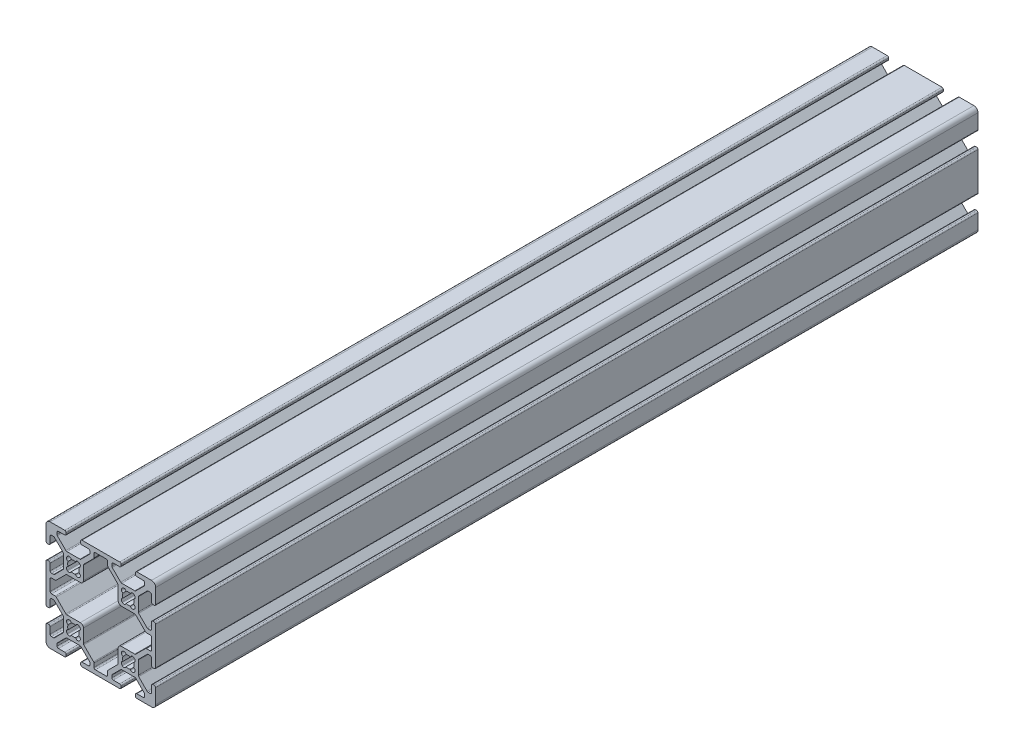
SolidWorks part; units mm, degrees
material "6105-T5 Aluminum"
ref_plane "Front Plane" through (0, 0, 0) normal (0, 0, 1) x (1, 0, 0)
ref_plane "Top Plane" through (0, 0, 0) normal (0, 1, 0) x (1, 0, 0)
ref_plane "Right Plane" through (0, 0, 0) normal (1, 0, 0) x (0, 0, -1)
sketch "Sketch1" plane through (0, 0, 0) normal (0, 0, 1) x (1, 0, 0)
  line L0 (-2.1249, 17.6955) -> (-2.3045, 17.8751)
  line L1 (-2.3045, 22.1249) -> (-2.1249, 22.3045)
  line L2 (2.1249, 22.3045) -> (2.3045, 22.1249)
  line L3 (2.3045, 17.8751) -> (2.1249, 17.6955)
  line L4 (-22.1249, 17.6955) -> (-22.3045, 17.8751)
  line L5 (-22.3045, 22.1249) -> (-22.1249, 22.3045)
  line L6 (-17.8751, 22.3045) -> (-17.6955, 22.1249)
  line L7 (-17.6955, 17.8751) -> (-17.8751, 17.6955)
  line L8 (-2.1249, -2.3045) -> (-2.3045, -2.1249)
  line L9 (-2.3045, 2.1249) -> (-2.1249, 2.3045)
  line L10 (2.1249, 2.3045) -> (2.3045, 2.1249)
  line L11 (2.3045, -2.1249) -> (2.1249, -2.3045)
  line L12 (-12.505, -7.992) -> (-12.505, -6.6448)
  line L13 (-12.6538, -6.2856) -> (-16.1962, -2.7431)
  line L14 (-16.345, -2.3839) -> (-16.345, 2.512)
  line L15 (-17.488, 3.655) -> (-22.3839, 3.655)
  line L16 (-22.7431, 3.8038) -> (-26.2856, 7.3462)
  line L17 (-26.6448, 7.495) -> (-27.992, 7.495)
  line L18 (-28.5, 8.003) -> (-28.5, 11.997)
  line L19 (-27.992, 12.505) -> (-26.6448, 12.505)
  line L20 (-26.2856, 12.6538) -> (-22.7431, 16.1962)
  line L21 (-22.3839, 16.345) -> (-17.488, 16.345)
  line L22 (-16.345, 17.488) -> (-16.345, 22.3839)
  line L23 (-16.1962, 22.7431) -> (-12.6538, 26.2856)
  line L24 (-12.505, 26.6448) -> (-12.505, 27.992)
  line L25 (-11.997, 28.5) -> (-8.003, 28.5)
  line L26 (-7.495, 27.992) -> (-7.495, 26.6448)
  line L27 (-7.3462, 26.2856) -> (-3.8038, 22.7431)
  line L28 (-3.655, 22.3839) -> (-3.655, 17.488)
  line L29 (-2.512, 16.345) -> (2.3839, 16.345)
  line L30 (2.7431, 16.1962) -> (6.2856, 12.6538)
  line L31 (6.6448, 12.505) -> (7.992, 12.505)
  line L32 (8.5, 11.997) -> (8.5, 8.003)
  line L33 (7.992, 7.495) -> (6.6448, 7.495)
  line L34 (6.2856, 7.3462) -> (2.7431, 3.8038)
  line L35 (2.3839, 3.655) -> (-2.512, 3.655)
  line L36 (-3.655, 2.512) -> (-3.655, -2.3839)
  line L37 (-3.8038, -2.7431) -> (-7.3462, -6.2856)
  line L38 (-7.495, -6.6448) -> (-7.495, -7.992)
  line L39 (-8.003, -8.5) -> (-11.997, -8.5)
  line L40 (-22.1249, -2.3045) -> (-22.3045, -2.1249)
  line L41 (-22.3045, 2.1249) -> (-22.1249, 2.3045)
  line L42 (-17.8751, 2.3045) -> (-17.6955, 2.1249)
  line L43 (-17.6955, -2.1249) -> (-17.8751, -2.3045)
  line L44 (-22.3839, -3.655) -> (-17.6161, -3.655)
  line L45 (-17.2569, -3.8038) -> (-14.1538, -6.9069)
  line L46 (-14.005, -7.2661) -> (-14.005, -7.992)
  line L47 (-14.513, -8.5) -> (-16.862, -8.5)
  line L48 (-17.37, -9.008) -> (-17.37, -9.492)
  line L49 (-16.862, -10) -> (-3.138, -10)
  line L50 (-2.63, -9.492) -> (-2.63, -9.008)
  line L51 (-3.138, -8.5) -> (-5.487, -8.5)
  line L52 (-5.995, -7.992) -> (-5.995, -7.2661)
  line L53 (-5.8462, -6.9069) -> (-2.7431, -3.8038)
  line L54 (-2.3839, -3.655) -> (2.3839, -3.655)
  line L55 (2.7431, -3.8038) -> (5.8462, -6.9069)
  line L56 (5.995, -7.2661) -> (5.995, -7.992)
  line L57 (5.487, -8.5) -> (3.138, -8.5)
  line L58 (2.63, -9.008) -> (2.63, -9.492)
  line L59 (3.138, -10) -> (8.5, -10)
  line L60 (10, -8.5) -> (10, -3.138)
  line L61 (9.492, -2.63) -> (9.008, -2.63)
  line L62 (8.5, -3.138) -> (8.5, -5.487)
  line L63 (7.992, -5.995) -> (7.2661, -5.995)
  line L64 (6.9069, -5.8462) -> (3.8038, -2.7431)
  line L65 (3.655, -2.3839) -> (3.655, 2.3839)
  line L66 (3.8038, 2.7431) -> (6.9069, 5.8462)
  line L67 (7.2661, 5.995) -> (7.992, 5.995)
  line L68 (8.5, 5.487) -> (8.5, 3.138)
  line L69 (9.008, 2.63) -> (9.492, 2.63)
  line L70 (10, 3.138) -> (10, 16.862)
  line L71 (9.492, 17.37) -> (9.008, 17.37)
  line L72 (8.5, 16.862) -> (8.5, 14.513)
  line L73 (7.992, 14.005) -> (7.2661, 14.005)
  line L74 (6.9069, 14.1538) -> (3.8038, 17.2569)
  line L75 (3.655, 17.6161) -> (3.655, 22.3839)
  line L76 (3.8038, 22.7431) -> (6.9069, 25.8462)
  line L77 (7.2661, 25.995) -> (7.992, 25.995)
  line L78 (8.5, 25.487) -> (8.5, 23.138)
  line L79 (9.008, 22.63) -> (9.492, 22.63)
  line L80 (10, 23.138) -> (10, 28.5)
  line L81 (8.5, 30) -> (3.138, 30)
  line L82 (2.63, 29.492) -> (2.63, 29.008)
  line L83 (3.138, 28.5) -> (5.487, 28.5)
  line L84 (5.995, 27.992) -> (5.995, 27.2661)
  line L85 (5.8462, 26.9069) -> (2.7431, 23.8038)
  line L86 (2.3839, 23.655) -> (-2.3839, 23.655)
  line L87 (-2.7431, 23.8038) -> (-5.8462, 26.9069)
  line L88 (-5.995, 27.2661) -> (-5.995, 27.992)
  line L89 (-5.487, 28.5) -> (-3.138, 28.5)
  line L90 (-2.63, 29.008) -> (-2.63, 29.492)
  line L91 (-3.138, 30) -> (-16.862, 30)
  line L92 (-17.37, 29.492) -> (-17.37, 29.008)
  line L93 (-16.862, 28.5) -> (-14.513, 28.5)
  line L94 (-14.005, 27.992) -> (-14.005, 27.2661)
  line L95 (-14.1538, 26.9069) -> (-17.2569, 23.8038)
  line L96 (-17.6161, 23.655) -> (-22.3839, 23.655)
  line L97 (-22.7431, 23.8038) -> (-25.8462, 26.9069)
  line L98 (-25.995, 27.2661) -> (-25.995, 27.992)
  line L99 (-25.487, 28.5) -> (-23.138, 28.5)
  line L100 (-22.63, 29.008) -> (-22.63, 29.492)
  line L101 (-23.138, 30) -> (-28.5, 30)
  line L102 (-30, 28.5) -> (-30, 23.138)
  line L103 (-29.492, 22.63) -> (-29.008, 22.63)
  line L104 (-28.5, 23.138) -> (-28.5, 25.487)
  line L105 (-27.992, 25.995) -> (-27.2661, 25.995)
  line L106 (-26.9069, 25.8462) -> (-23.8038, 22.7431)
  line L107 (-23.655, 22.3839) -> (-23.655, 17.6161)
  line L108 (-23.8038, 17.2569) -> (-26.9069, 14.1538)
  line L109 (-27.2661, 14.005) -> (-27.992, 14.005)
  line L110 (-28.5, 14.513) -> (-28.5, 16.862)
  line L111 (-29.008, 17.37) -> (-29.492, 17.37)
  line L112 (-30, 16.862) -> (-30, 3.138)
  line L113 (-29.492, 2.63) -> (-29.008, 2.63)
  line L114 (-28.5, 3.138) -> (-28.5, 5.487)
  line L115 (-27.992, 5.995) -> (-27.2661, 5.995)
  line L116 (-26.9069, 5.8462) -> (-23.8038, 2.7431)
  line L117 (-23.655, 2.3839) -> (-23.655, -2.3839)
  line L118 (-23.8038, -2.7431) -> (-26.9069, -5.8462)
  line L119 (-27.2661, -5.995) -> (-27.992, -5.995)
  line L120 (-28.5, -5.487) -> (-28.5, -3.138)
  line L121 (-29.008, -2.63) -> (-29.492, -2.63)
  line L122 (-30, -3.138) -> (-30, -8.5)
  line L123 (-28.5, -10) -> (-23.138, -10)
  line L124 (-22.63, -9.492) -> (-22.63, -9.008)
  line L125 (-23.138, -8.5) -> (-25.487, -8.5)
  line L126 (-25.995, -7.992) -> (-25.995, -7.2661)
  line L127 (-25.8462, -6.9069) -> (-22.7431, -3.8038)
  arc A0 (-1.9351, 19.196) -> (-2.3045, 17.8751) centre (-1.748, 18.4316) ccw
  arc A1 (-1.9351, 20.804) -> (-1.9351, 19.196) centre (0, 20) ccw
  arc A2 (-2.3045, 22.1249) -> (-1.9351, 20.804) centre (-1.748, 21.5684) ccw
  arc A3 (-0.804, 21.9351) -> (-2.1249, 22.3045) centre (-1.5684, 21.748) ccw
  arc A4 (0.804, 21.9351) -> (-0.804, 21.9351) centre (0, 20) ccw
  arc A5 (2.1249, 22.3045) -> (0.804, 21.9351) centre (1.5684, 21.748) ccw
  arc A6 (1.9351, 20.804) -> (2.3045, 22.1249) centre (1.748, 21.5684) ccw
  arc A7 (1.9351, 19.196) -> (1.9351, 20.804) centre (0, 20) ccw
  arc A8 (2.3045, 17.8751) -> (1.9351, 19.196) centre (1.748, 18.4316) ccw
  arc A9 (0.804, 18.0649) -> (2.1249, 17.6955) centre (1.5684, 18.252) ccw
  arc A10 (-0.804, 18.0649) -> (0.804, 18.0649) centre (0, 20) ccw
  arc A11 (-2.1249, 17.6955) -> (-0.804, 18.0649) centre (-1.5684, 18.252) ccw
  arc A12 (-21.9351, 19.196) -> (-22.3045, 17.8751) centre (-21.748, 18.4316) ccw
  arc A13 (-21.9351, 20.804) -> (-21.9351, 19.196) centre (-20, 20) ccw
  arc A14 (-22.3045, 22.1249) -> (-21.9351, 20.804) centre (-21.748, 21.5684) ccw
  arc A15 (-20.804, 21.9351) -> (-22.1249, 22.3045) centre (-21.5684, 21.748) ccw
  arc A16 (-19.196, 21.9351) -> (-20.804, 21.9351) centre (-20, 20) ccw
  arc A17 (-17.8751, 22.3045) -> (-19.196, 21.9351) centre (-18.4316, 21.748) ccw
  arc A18 (-18.0649, 20.804) -> (-17.6955, 22.1249) centre (-18.252, 21.5684) ccw
  arc A19 (-18.0649, 19.196) -> (-18.0649, 20.804) centre (-20, 20) ccw
  arc A20 (-17.6955, 17.8751) -> (-18.0649, 19.196) centre (-18.252, 18.4316) ccw
  arc A21 (-19.196, 18.0649) -> (-17.8751, 17.6955) centre (-18.4316, 18.252) ccw
  arc A22 (-20.804, 18.0649) -> (-19.196, 18.0649) centre (-20, 20) ccw
  arc A23 (-22.1249, 17.6955) -> (-20.804, 18.0649) centre (-21.5684, 18.252) ccw
  arc A24 (-1.9351, -0.804) -> (-2.3045, -2.1249) centre (-1.748, -1.5684) ccw
  arc A25 (-1.9351, 0.804) -> (-1.9351, -0.804) centre (0, 0) ccw
  arc A26 (-2.3045, 2.1249) -> (-1.9351, 0.804) centre (-1.748, 1.5684) ccw
  arc A27 (-0.804, 1.9351) -> (-2.1249, 2.3045) centre (-1.5684, 1.748) ccw
  arc A28 (0.804, 1.9351) -> (-0.804, 1.9351) centre (0, 0) ccw
  arc A29 (2.1249, 2.3045) -> (0.804, 1.9351) centre (1.5684, 1.748) ccw
  arc A30 (1.9351, 0.804) -> (2.3045, 2.1249) centre (1.748, 1.5684) ccw
  arc A31 (1.9351, -0.804) -> (1.9351, 0.804) centre (0, 0) ccw
  arc A32 (2.3045, -2.1249) -> (1.9351, -0.804) centre (1.748, -1.5684) ccw
  arc A33 (0.804, -1.9351) -> (2.1249, -2.3045) centre (1.5684, -1.748) ccw
  arc A34 (-0.804, -1.9351) -> (0.804, -1.9351) centre (0, 0) ccw
  arc A35 (-2.1249, -2.3045) -> (-0.804, -1.9351) centre (-1.5684, -1.748) ccw
  arc A36 (-12.505, -7.992) -> (-11.997, -8.5) centre (-11.997, -7.992) ccw
  arc A37 (-12.505, -6.6448) -> (-12.6538, -6.2856) centre (-13.013, -6.6448) ccw
  arc A38 (-16.345, -2.3839) -> (-16.1962, -2.7431) centre (-15.837, -2.3839) ccw
  arc A39 (-16.345, 2.512) -> (-17.488, 3.655) centre (-17.488, 2.512) ccw
  arc A40 (-22.7431, 3.8038) -> (-22.3839, 3.655) centre (-22.3839, 4.163) ccw
  arc A41 (-26.2856, 7.3462) -> (-26.6448, 7.495) centre (-26.6448, 6.987) ccw
  arc A42 (-28.5, 8.003) -> (-27.992, 7.495) centre (-27.992, 8.003) ccw
  arc A43 (-27.992, 12.505) -> (-28.5, 11.997) centre (-27.992, 11.997) ccw
  arc A44 (-26.6448, 12.505) -> (-26.2856, 12.6538) centre (-26.6448, 13.013) ccw
  arc A45 (-22.3839, 16.345) -> (-22.7431, 16.1962) centre (-22.3839, 15.837) ccw
  arc A46 (-17.488, 16.345) -> (-16.345, 17.488) centre (-17.488, 17.488) ccw
  arc A47 (-16.1962, 22.7431) -> (-16.345, 22.3839) centre (-15.837, 22.3839) ccw
  arc A48 (-12.6538, 26.2856) -> (-12.505, 26.6448) centre (-13.013, 26.6448) ccw
  arc A49 (-11.997, 28.5) -> (-12.505, 27.992) centre (-11.997, 27.992) ccw
  arc A50 (-7.495, 27.992) -> (-8.003, 28.5) centre (-8.003, 27.992) ccw
  arc A51 (-7.495, 26.6448) -> (-7.3462, 26.2856) centre (-6.987, 26.6448) ccw
  arc A52 (-3.655, 22.3839) -> (-3.8038, 22.7431) centre (-4.163, 22.3839) ccw
  arc A53 (-3.655, 17.488) -> (-2.512, 16.345) centre (-2.512, 17.488) ccw
  arc A54 (2.7431, 16.1962) -> (2.3839, 16.345) centre (2.3839, 15.837) ccw
  arc A55 (6.2856, 12.6538) -> (6.6448, 12.505) centre (6.6448, 13.013) ccw
  arc A56 (8.5, 11.997) -> (7.992, 12.505) centre (7.992, 11.997) ccw
  arc A57 (7.992, 7.495) -> (8.5, 8.003) centre (7.992, 8.003) ccw
  arc A58 (6.6448, 7.495) -> (6.2856, 7.3462) centre (6.6448, 6.987) ccw
  arc A59 (2.3839, 3.655) -> (2.7431, 3.8038) centre (2.3839, 4.163) ccw
  arc A60 (-2.512, 3.655) -> (-3.655, 2.512) centre (-2.512, 2.512) ccw
  arc A61 (-3.8038, -2.7431) -> (-3.655, -2.3839) centre (-4.163, -2.3839) ccw
  arc A62 (-7.3462, -6.2856) -> (-7.495, -6.6448) centre (-6.987, -6.6448) ccw
  arc A63 (-8.003, -8.5) -> (-7.495, -7.992) centre (-8.003, -7.992) ccw
  arc A64 (-21.9351, -0.804) -> (-22.3045, -2.1249) centre (-21.748, -1.5684) ccw
  arc A65 (-21.9351, 0.804) -> (-21.9351, -0.804) centre (-20, 0) ccw
  arc A66 (-22.3045, 2.1249) -> (-21.9351, 0.804) centre (-21.748, 1.5684) ccw
  arc A67 (-20.804, 1.9351) -> (-22.1249, 2.3045) centre (-21.5684, 1.748) ccw
  arc A68 (-19.196, 1.9351) -> (-20.804, 1.9351) centre (-20, 0) ccw
  arc A69 (-17.8751, 2.3045) -> (-19.196, 1.9351) centre (-18.4316, 1.748) ccw
  arc A70 (-18.0649, 0.804) -> (-17.6955, 2.1249) centre (-18.252, 1.5684) ccw
  arc A71 (-18.0649, -0.804) -> (-18.0649, 0.804) centre (-20, 0) ccw
  arc A72 (-17.6955, -2.1249) -> (-18.0649, -0.804) centre (-18.252, -1.5684) ccw
  arc A73 (-19.196, -1.9351) -> (-17.8751, -2.3045) centre (-18.4316, -1.748) ccw
  arc A74 (-20.804, -1.9351) -> (-19.196, -1.9351) centre (-20, 0) ccw
  arc A75 (-22.1249, -2.3045) -> (-20.804, -1.9351) centre (-21.5684, -1.748) ccw
  arc A76 (-22.3839, -3.655) -> (-22.7431, -3.8038) centre (-22.3839, -4.163) ccw
  arc A77 (-17.2569, -3.8038) -> (-17.6161, -3.655) centre (-17.6161, -4.163) ccw
  arc A78 (-14.005, -7.2661) -> (-14.1538, -6.9069) centre (-14.513, -7.2661) ccw
  arc A79 (-14.513, -8.5) -> (-14.005, -7.992) centre (-14.513, -7.992) ccw
  arc A80 (-16.862, -8.5) -> (-17.37, -9.008) centre (-16.862, -9.008) ccw
  arc A81 (-17.37, -9.492) -> (-16.862, -10) centre (-16.862, -9.492) ccw
  arc A82 (-3.138, -10) -> (-2.63, -9.492) centre (-3.138, -9.492) ccw
  arc A83 (-2.63, -9.008) -> (-3.138, -8.5) centre (-3.138, -9.008) ccw
  arc A84 (-5.995, -7.992) -> (-5.487, -8.5) centre (-5.487, -7.992) ccw
  arc A85 (-5.8462, -6.9069) -> (-5.995, -7.2661) centre (-5.487, -7.2661) ccw
  arc A86 (-2.3839, -3.655) -> (-2.7431, -3.8038) centre (-2.3839, -4.163) ccw
  arc A87 (2.7431, -3.8038) -> (2.3839, -3.655) centre (2.3839, -4.163) ccw
  arc A88 (5.995, -7.2661) -> (5.8462, -6.9069) centre (5.487, -7.2661) ccw
  arc A89 (5.487, -8.5) -> (5.995, -7.992) centre (5.487, -7.992) ccw
  arc A90 (3.138, -8.5) -> (2.63, -9.008) centre (3.138, -9.008) ccw
  arc A91 (2.63, -9.492) -> (3.138, -10) centre (3.138, -9.492) ccw
  arc A92 (8.5, -10) -> (10, -8.5) centre (8.5, -8.5) ccw
  arc A93 (10, -3.138) -> (9.492, -2.63) centre (9.492, -3.138) ccw
  arc A94 (9.008, -2.63) -> (8.5, -3.138) centre (9.008, -3.138) ccw
  arc A95 (7.992, -5.995) -> (8.5, -5.487) centre (7.992, -5.487) ccw
  arc A96 (6.9069, -5.8462) -> (7.2661, -5.995) centre (7.2661, -5.487) ccw
  arc A97 (3.655, -2.3839) -> (3.8038, -2.7431) centre (4.163, -2.3839) ccw
  arc A98 (3.8038, 2.7431) -> (3.655, 2.3839) centre (4.163, 2.3839) ccw
  arc A99 (7.2661, 5.995) -> (6.9069, 5.8462) centre (7.2661, 5.487) ccw
  arc A100 (8.5, 5.487) -> (7.992, 5.995) centre (7.992, 5.487) ccw
  arc A101 (8.5, 3.138) -> (9.008, 2.63) centre (9.008, 3.138) ccw
  arc A102 (9.492, 2.63) -> (10, 3.138) centre (9.492, 3.138) ccw
  arc A103 (10, 16.862) -> (9.492, 17.37) centre (9.492, 16.862) ccw
  arc A104 (9.008, 17.37) -> (8.5, 16.862) centre (9.008, 16.862) ccw
  arc A105 (7.992, 14.005) -> (8.5, 14.513) centre (7.992, 14.513) ccw
  arc A106 (6.9069, 14.1538) -> (7.2661, 14.005) centre (7.2661, 14.513) ccw
  arc A107 (3.655, 17.6161) -> (3.8038, 17.2569) centre (4.163, 17.6161) ccw
  arc A108 (3.8038, 22.7431) -> (3.655, 22.3839) centre (4.163, 22.3839) ccw
  arc A109 (7.2661, 25.995) -> (6.9069, 25.8462) centre (7.2661, 25.487) ccw
  arc A110 (8.5, 25.487) -> (7.992, 25.995) centre (7.992, 25.487) ccw
  arc A111 (8.5, 23.138) -> (9.008, 22.63) centre (9.008, 23.138) ccw
  arc A112 (9.492, 22.63) -> (10, 23.138) centre (9.492, 23.138) ccw
  arc A113 (10, 28.5) -> (8.5, 30) centre (8.5, 28.5) ccw
  arc A114 (3.138, 30) -> (2.63, 29.492) centre (3.138, 29.492) ccw
  arc A115 (2.63, 29.008) -> (3.138, 28.5) centre (3.138, 29.008) ccw
  arc A116 (5.995, 27.992) -> (5.487, 28.5) centre (5.487, 27.992) ccw
  arc A117 (5.8462, 26.9069) -> (5.995, 27.2661) centre (5.487, 27.2661) ccw
  arc A118 (2.3839, 23.655) -> (2.7431, 23.8038) centre (2.3839, 24.163) ccw
  arc A119 (-2.7431, 23.8038) -> (-2.3839, 23.655) centre (-2.3839, 24.163) ccw
  arc A120 (-5.995, 27.2661) -> (-5.8462, 26.9069) centre (-5.487, 27.2661) ccw
  arc A121 (-5.487, 28.5) -> (-5.995, 27.992) centre (-5.487, 27.992) ccw
  arc A122 (-3.138, 28.5) -> (-2.63, 29.008) centre (-3.138, 29.008) ccw
  arc A123 (-2.63, 29.492) -> (-3.138, 30) centre (-3.138, 29.492) ccw
  arc A124 (-16.862, 30) -> (-17.37, 29.492) centre (-16.862, 29.492) ccw
  arc A125 (-17.37, 29.008) -> (-16.862, 28.5) centre (-16.862, 29.008) ccw
  arc A126 (-14.005, 27.992) -> (-14.513, 28.5) centre (-14.513, 27.992) ccw
  arc A127 (-14.1538, 26.9069) -> (-14.005, 27.2661) centre (-14.513, 27.2661) ccw
  arc A128 (-17.6161, 23.655) -> (-17.2569, 23.8038) centre (-17.6161, 24.163) ccw
  arc A129 (-22.7431, 23.8038) -> (-22.3839, 23.655) centre (-22.3839, 24.163) ccw
  arc A130 (-25.995, 27.2661) -> (-25.8462, 26.9069) centre (-25.487, 27.2661) ccw
  arc A131 (-25.487, 28.5) -> (-25.995, 27.992) centre (-25.487, 27.992) ccw
  arc A132 (-23.138, 28.5) -> (-22.63, 29.008) centre (-23.138, 29.008) ccw
  arc A133 (-22.63, 29.492) -> (-23.138, 30) centre (-23.138, 29.492) ccw
  arc A134 (-28.5, 30) -> (-30, 28.5) centre (-28.5, 28.5) ccw
  arc A135 (-30, 23.138) -> (-29.492, 22.63) centre (-29.492, 23.138) ccw
  arc A136 (-29.008, 22.63) -> (-28.5, 23.138) centre (-29.008, 23.138) ccw
  arc A137 (-27.992, 25.995) -> (-28.5, 25.487) centre (-27.992, 25.487) ccw
  arc A138 (-26.9069, 25.8462) -> (-27.2661, 25.995) centre (-27.2661, 25.487) ccw
  arc A139 (-23.655, 22.3839) -> (-23.8038, 22.7431) centre (-24.163, 22.3839) ccw
  arc A140 (-23.8038, 17.2569) -> (-23.655, 17.6161) centre (-24.163, 17.6161) ccw
  arc A141 (-27.2661, 14.005) -> (-26.9069, 14.1538) centre (-27.2661, 14.513) ccw
  arc A142 (-28.5, 14.513) -> (-27.992, 14.005) centre (-27.992, 14.513) ccw
  arc A143 (-28.5, 16.862) -> (-29.008, 17.37) centre (-29.008, 16.862) ccw
  arc A144 (-29.492, 17.37) -> (-30, 16.862) centre (-29.492, 16.862) ccw
  arc A145 (-30, 3.138) -> (-29.492, 2.63) centre (-29.492, 3.138) ccw
  arc A146 (-29.008, 2.63) -> (-28.5, 3.138) centre (-29.008, 3.138) ccw
  arc A147 (-27.992, 5.995) -> (-28.5, 5.487) centre (-27.992, 5.487) ccw
  arc A148 (-26.9069, 5.8462) -> (-27.2661, 5.995) centre (-27.2661, 5.487) ccw
  arc A149 (-23.655, 2.3839) -> (-23.8038, 2.7431) centre (-24.163, 2.3839) ccw
  arc A150 (-23.8038, -2.7431) -> (-23.655, -2.3839) centre (-24.163, -2.3839) ccw
  arc A151 (-27.2661, -5.995) -> (-26.9069, -5.8462) centre (-27.2661, -5.487) ccw
  arc A152 (-28.5, -5.487) -> (-27.992, -5.995) centre (-27.992, -5.487) ccw
  arc A153 (-28.5, -3.138) -> (-29.008, -2.63) centre (-29.008, -3.138) ccw
  arc A154 (-29.492, -2.63) -> (-30, -3.138) centre (-29.492, -3.138) ccw
  arc A155 (-30, -8.5) -> (-28.5, -10) centre (-28.5, -8.5) ccw
  arc A156 (-23.138, -10) -> (-22.63, -9.492) centre (-23.138, -9.492) ccw
  arc A157 (-22.63, -9.008) -> (-23.138, -8.5) centre (-23.138, -9.008) ccw
  arc A158 (-25.995, -7.992) -> (-25.487, -8.5) centre (-25.487, -7.992) ccw
  arc A159 (-25.8462, -6.9069) -> (-25.995, -7.2661) centre (-25.487, -7.2661) ccw
extrude "Extrude1" add sketch "Sketch1" against normal blind 300
